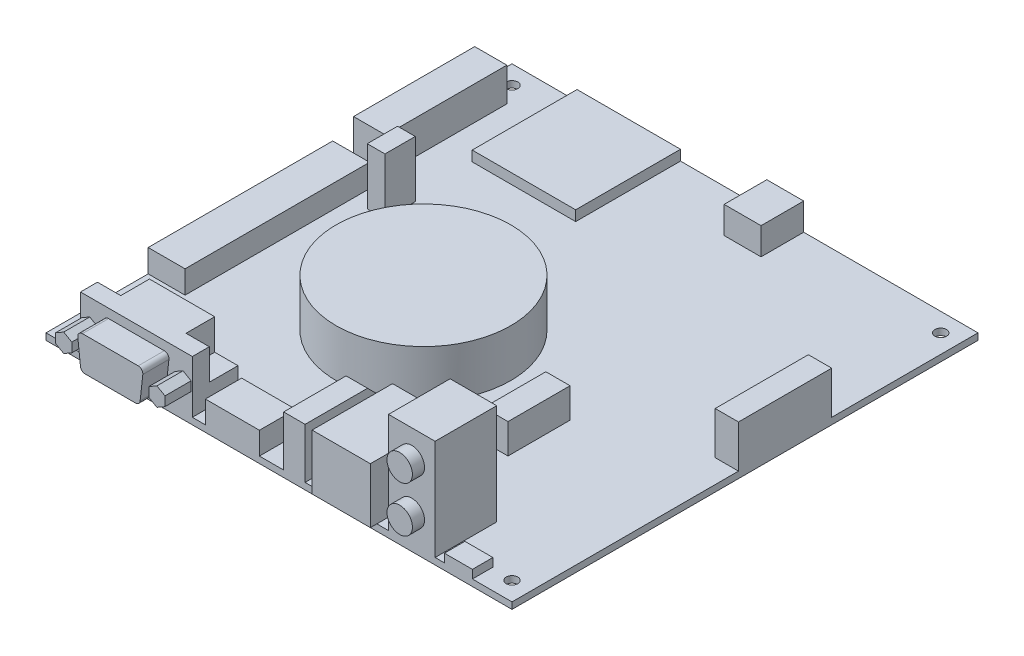
SolidWorks part; units mm, degrees
ref_plane "Front Plane" through (0, 0, 0) normal (0, 0, 1) x (1, 0, 0)
ref_plane "Top Plane" through (0, 0, 0) normal (0, 1, 0) x (1, 0, 0)
ref_plane "Right Plane" through (0, 0, 0) normal (1, 0, 0) x (0, 0, -1)
sketch "Sketch1" plane through (0, 0, 0) normal (0, 1, 0) x (1, 0, 0)
  line L0 (5.08, 5.08) -> (5.08, 121.92) construction
  line L1 (0, 0) -> (127, 0)
  line L2 (0, 0) -> (0, 127)
  line L3 (0, 127) -> (127, 127)
  line L4 (127, 0) -> (127, 127)
  line L5 (5.08, 121.92) -> (121.92, 121.92) construction
  line L6 (121.92, 5.08) -> (121.92, 121.92) construction
  line L7 (5.08, 5.08) -> (121.92, 5.08) construction
  circle A0 centre (5.08, 121.92) radius 1.5875
  circle A1 centre (121.92, 121.92) radius 1.5875
  circle A2 centre (121.92, 5.08) radius 1.5875
  circle A3 centre (5.08, 5.08) radius 1.5875
  dimension "D3" = 3.175
  dimension "D1" = 127
  dimension "D2" = 5.08
extrude "Boss-Extrude1" add sketch "Sketch1" along normal blind 1.778
sketch "Sketch2" plane through (0, 1.778, 0) normal (0, 1, 0) x (1, 0, 0)
  line L0 (127, 127) -> (0, 127) construction
  line L1 (17.7292, 127) -> (45.9232, 127)
  line L2 (17.7292, 127) -> (17.7292, 98.425)
  line L3 (17.7292, 98.425) -> (45.9232, 98.425)
  line L4 (45.9232, 127) -> (45.9232, 98.425)
  line L5 (0, 127) -> (0, 0) construction
  dimension "D1" = 28.194
  dimension "D2" = 28.575
  dimension "D3" = 45.9232
extrude "Boss-Extrude2" add sketch "Sketch2" along normal blind 2.794
sketch "Sketch3" plane through (0, 1.778, 0) normal (0, 1, 0) x (1, 0, 0)
  line L0 (127, 127) -> (45.9232, 127) construction
  line L1 (69.4436, 127) -> (79.502, 127)
  line L2 (69.4436, 127) -> (69.4436, 115.3668)
  line L3 (69.4436, 115.3668) -> (79.502, 115.3668)
  line L4 (79.502, 127) -> (79.502, 115.3668)
  line L5 (127, 0) -> (127, 127) construction
  dimension "D1" = 10.0584
  dimension "D2" = 11.6332
  dimension "D3" = 57.5564
extrude "Boss-Extrude3" add sketch "Sketch3" along normal blind 7.366
sketch "Sketch4" plane through (0, 1.778, 0) normal (0, 1, 0) x (1, 0, 0)
  line L0 (127, 0) -> (127, 127) construction
  line L1 (127, 87.122) -> (120.65, 87.122)
  line L2 (127, 87.122) -> (127, 61.722)
  line L3 (127, 61.722) -> (120.65, 61.722)
  line L4 (120.65, 87.122) -> (120.65, 61.722)
  line L5 (127, 127) -> (79.502, 127) construction
  dimension "D1" = 25.4
  dimension "D2" = 6.35
  dimension "D3" = 65.278
extrude "Boss-Extrude4" add sketch "Sketch4" along normal blind 11.6078
sketch "Sketch5" plane through (0, 1.778, 0) normal (0, 1, 0) x (1, 0, 0)
  line L0 (0, 127) -> (0, 0) construction
  line L1 (0, 116.84) -> (8.763, 116.84)
  line L2 (0, 116.84) -> (0, 83.82)
  line L3 (0, 83.82) -> (8.763, 83.82)
  line L4 (8.763, 116.84) -> (8.763, 83.82)
  line L5 (17.7292, 127) -> (0, 127) construction
  dimension "D1" = 8.763
  dimension "D2" = 33.02
  dimension "D3" = 43.18
extrude "Boss-Extrude5" add sketch "Sketch5" along normal blind 9.144
sketch "Sketch6" plane through (0, 1.778, 0) normal (0, 1, 0) x (1, 0, 0)
  line L0 (0, 83.82) -> (0, 0) construction
  line L1 (0, 27.8384) -> (10.0584, 27.8384)
  line L2 (0, 27.8384) -> (0, 78.1304)
  line L3 (0, 78.1304) -> (10.0584, 78.1304)
  line L4 (10.0584, 27.8384) -> (10.0584, 78.1304)
  line L5 (0, 0) -> (127, 0) construction
  dimension "D1" = 10.0584
  dimension "D2" = 50.292
  dimension "D3" = 78.1304
extrude "Boss-Extrude6" add sketch "Sketch6" along normal blind 6.223 contours L3 L4 L1 L2
sketch "Sketch7" plane through (0, 1.778, 0) normal (0, 1, 0) x (1, 0, 0)
  line L0 (0, 83.82) -> (0, 78.1304) construction
  line L1 (14.5288, 81.28) -> (19.3548, 81.28)
  line L2 (14.5288, 81.28) -> (14.5288, 73.025)
  line L3 (14.5288, 73.025) -> (19.3548, 73.025)
  line L4 (19.3548, 81.28) -> (19.3548, 73.025)
  line L5 (17.7292, 127) -> (0, 127) construction
  point P4 (0, 80.9752)
  dimension "D1" = 4.826
  dimension "D2" = 8.255
  dimension "D3" = 19.3548
  dimension "D4" = 53.975
extrude "Boss-Extrude7" add sketch "Sketch7" along normal blind 15.3924 contours L1 L4 L3 L2
sketch "Sketch8" plane through (0, 1.778, 0) normal (0, 1, 0) x (1, 0, 0)
  line L0 (0, 0) -> (127, 0) construction
  line L1 (108.585, 0) -> (116.205, 0)
  line L2 (108.585, 0) -> (108.585, 5.588)
  line L3 (108.585, 5.588) -> (116.205, 5.588)
  line L4 (116.205, 0) -> (116.205, 5.588)
  line L5 (127, 0) -> (127, 61.722) construction
  dimension "D1" = 7.62
  dimension "D2" = 5.588
  dimension "D3" = 18.415
extrude "Boss-Extrude8" add sketch "Sketch8" along normal blind 2.286
sketch "Sketch9" plane through (0, 1.778, 0) normal (0, 1, 0) x (1, 0, 0)
  line L0 (0, 27.8384) -> (0, 78.1304) construction
  line L1 (69.4436, 127) -> (45.9232, 127) construction
  circle A0 centre (50.8, 52.07) radius 23.8125
  dimension "D1" = 47.625
  dimension "D2" = 50.8
  dimension "D3" = 74.93
extrude "Boss-Extrude9" add sketch "Sketch9" along normal blind 12.954
sketch "Sketch10" plane through (0, 1.778, 0) normal (0, 1, 0) x (1, 0, 0)
  line L0 (0, 0) -> (108.585, 0) construction
  line L1 (106.045, 0) -> (93.345, 0)
  line L2 (106.045, 0) -> (106.045, 16.7894)
  line L3 (106.045, 16.7894) -> (93.345, 16.7894)
  line L4 (93.345, 0) -> (93.345, 16.7894)
  line L5 (127, 0) -> (127, 61.722) construction
  dimension "D1" = 12.7
  dimension "D2" = 16.7894
  dimension "D3" = 33.655
extrude "Boss-Extrude10" add sketch "Sketch10" along normal blind 27.432
sketch "Sketch11" plane through (0, 0, 0) normal (0, 0, 1) x (1, 0, 0)
  line L0 (99.695, 21.59) -> (99.695, 29.21) construction
  line L1 (93.345, 29.21) -> (106.045, 29.21) construction
  line L2 (99.695, 21.59) -> (99.695, 9.144) construction
  line L3 (99.695, 9.144) -> (99.695, 0) construction
  line L4 (0, 0) -> (127, 0) construction
  circle A0 centre (99.695, 21.59) radius 3.4671
  circle A1 centre (99.695, 9.144) radius 3.4671
  dimension "D1" = 6.9342
  dimension "D2" = 7.62
  dimension "D3" = 12.446
extrude "Boss-Extrude11" add sketch "Sketch11" along normal blind 3.302
sketch "Sketch12" plane through (0, 1.778, 0) normal (0, 1, 0) x (1, 0, 0)
  line L1 (90.17, -1.778) -> (74.295, -1.778)
  line L2 (90.17, -1.778) -> (90.17, 20.1422)
  line L3 (90.17, 20.1422) -> (74.295, 20.1422)
  line L4 (74.295, -1.778) -> (74.295, 20.1422)
  line L5 (0, 0) -> (93.345, 0) construction
  line L6 (106.045, 0) -> (106.045, 16.7894) construction
  dimension "D1" = 15.875
  dimension "D2" = 21.9202
  dimension "D3" = 1.778
  dimension "D4" = 31.75
extrude "Boss-Extrude12" add sketch "Sketch12" along normal blind 15.0876
sketch "Sketch13" plane through (0, 1.778, 0) normal (0, 1, 0) x (1, 0, 0)
  line L0 (0, 0) -> (74.295, 0) construction
  line L1 (64.77, 0) -> (70.612, 0)
  line L2 (64.77, 0) -> (64.77, 25.4)
  line L3 (64.77, 25.4) -> (70.612, 25.4)
  line L4 (70.612, 0) -> (70.612, 25.4)
  line L5 (90.17, 0) -> (90.17, 20.1422) construction
  point P6 (90.17, 10.0711)
  dimension "D1" = 5.842
  dimension "D2" = 25.4
  dimension "D3" = 25.4
extrude "Boss-Extrude13" add sketch "Sketch13" along normal blind 13.716 contours L2 L3 L4 L1
chamfer "Chamfer1" distance 8.382 angle 45 1 edges at (67.691, 15.494, -25.4)
sketch "Sketch14" plane through (0, 1.778, 0) normal (0, 1, 0) x (1, 0, 0)
  line L0 (0, 0) -> (64.77, 0) construction
  line L1 (43.434, 0) -> (58.166, 0)
  line L2 (43.434, 0) -> (43.434, 9.8806)
  line L3 (43.434, 9.8806) -> (58.166, 9.8806)
  line L4 (58.166, 0) -> (58.166, 9.8806)
  line L5 (70.612, 0) -> (70.612, 17.018) construction
  dimension "D1" = 14.732
  dimension "D2" = 9.8806
  dimension "D3" = 27.178
extrude "Boss-Extrude14" add sketch "Sketch14" along normal blind 6.096
sketch "Sketch15" plane through (0, 1.778, 0) normal (0, 1, 0) x (1, 0, 0)
  line L0 (127, 0) -> (127, 61.722) construction
  line L1 (85.4202, 50.8) -> (92.0242, 50.8)
  line L2 (85.4202, 50.8) -> (85.4202, 33.8836)
  line L3 (85.4202, 33.8836) -> (92.0242, 33.8836)
  line L4 (92.0242, 50.8) -> (92.0242, 33.8836)
  line L5 (116.205, 0) -> (127, 0) construction
  dimension "D1" = 16.9164
  dimension "D2" = 6.604
  dimension "D3" = 41.5798
  dimension "D4" = 50.8
extrude "Boss-Extrude15" add sketch "Sketch15" along normal blind 8.128 contours L1 L4 L3 L2
sketch "Sketch16" plane through (0, 1.778, 0) normal (0, 1, 0) x (1, 0, 0)
  line L0 (0, 0) -> (43.434, 0) construction
  line L1 (9.398, 0) -> (39.878, 0)
  line L2 (9.398, 0) -> (9.398, 12.446)
  line L3 (9.398, 12.446) -> (39.878, 12.446)
  line L4 (39.878, 0) -> (39.878, 12.446)
  line L5 (0, 27.8384) -> (0, 0) construction
  dimension "D1" = 30.48
  dimension "D2" = 12.446
  dimension "D3" = 39.878
extrude "Boss-Extrude16" add sketch "Sketch16" along normal blind 14.351
sketch "Sketch17" plane through (0, 16.129, 0) normal (0, 1, 0) x (1, 0, 0)
  line L0 (9.398, 0) -> (39.878, 0) construction
  line L1 (9.398, 12.446) -> (15.748, 12.446)
  line L2 (9.398, 12.446) -> (9.398, 4.6228)
  line L3 (9.398, 4.6228) -> (15.748, 4.6228)
  line L4 (15.748, 12.446) -> (15.748, 4.6228)
  line L5 (39.878, 12.446) -> (33.528, 12.446)
  line L6 (39.878, 12.446) -> (39.878, 4.6228)
  line L7 (39.878, 4.6228) -> (33.528, 4.6228)
  line L8 (33.528, 12.446) -> (33.528, 4.6228)
  dimension "D1" = 6.35
  dimension "D2" = 6.35
  dimension "D3" = 4.6228
  dimension "D4" = 4.6228
extrude "Cut-Extrude1" cut sketch "Sketch17" against normal blind 8.382
sketch "Sketch18" plane through (0, 0, 0) normal (0, 0, 1) x (1, 0, 0)
  line L0 (9.398, 8.9535) -> (11.938, 8.9535) construction
  line L1 (11.938, 11.4935) -> (9.7383, 10.2235)
  line L2 (9.7383, 10.2235) -> (9.7383, 7.6835)
  line L3 (9.7383, 7.6835) -> (11.938, 6.4135)
  line L4 (11.938, 6.4135) -> (14.1377, 7.6835)
  line L5 (14.1377, 7.6835) -> (14.1377, 10.2235)
  line L6 (14.1377, 10.2235) -> (11.938, 11.4935)
  line L7 (37.338, 11.4935) -> (35.1383, 10.2235)
  line L8 (35.1383, 10.2235) -> (35.1383, 7.6835)
  line L9 (35.1383, 7.6835) -> (37.338, 6.4135)
  line L10 (37.338, 6.4135) -> (39.5377, 7.6835)
  line L11 (39.5377, 7.6835) -> (39.5377, 10.2235)
  line L12 (39.5377, 10.2235) -> (37.338, 11.4935)
  line L13 (9.398, 16.129) -> (9.398, 1.778) construction
  line L14 (11.938, 8.9535) -> (37.338, 8.9535) construction
  line L15 (37.338, 8.9535) -> (39.878, 8.9535) construction
  line L16 (39.878, 16.129) -> (39.878, 1.778) construction
  line L17 (17.0399, 13.6657) -> (32.2361, 13.6657)
  line L18 (33.4983, 12.2555) -> (32.7645, 5.6515)
  line L19 (31.5023, 4.5217) -> (17.7737, 4.5217)
  line L20 (16.5115, 5.6515) -> (15.7777, 12.2555)
  line L21 (24.638, 16.129) -> (24.638, 13.6657) construction
  line L22 (9.398, 16.129) -> (39.878, 16.129) construction
  circle A0 centre (11.938, 8.9535) radius 2.1997 construction
  circle A1 centre (37.338, 8.9535) radius 2.1997 construction
  arc A2 (32.2361, 13.6657) -> (33.4983, 12.2555) centre (32.2361, 12.3957) cw
  arc A3 (32.7645, 5.6515) -> (31.5023, 4.5217) centre (31.5023, 5.7917) cw
  arc A4 (17.7737, 4.5217) -> (16.5115, 5.6515) centre (17.7737, 5.7917) cw
  arc A5 (17.0399, 13.6657) -> (15.7777, 12.2555) centre (17.0399, 12.3957) ccw
  point P24 (16.1446, 8.9535)
  point P33 (33.655, 13.6657)
  point P36 (32.639, 4.5217)
  point P39 (16.637, 4.5217)
  point P42 (15.621, 13.6657)
  dimension "D6" = 1.27
  dimension "D1" = 5.08
  dimension "D2" = 2.54
  dimension "D3" = 18.034
  dimension "D4" = 16.002
  dimension "D5" = 9.144
extrude "Boss-Extrude17" add sketch "Sketch18" along normal blind 7.112
